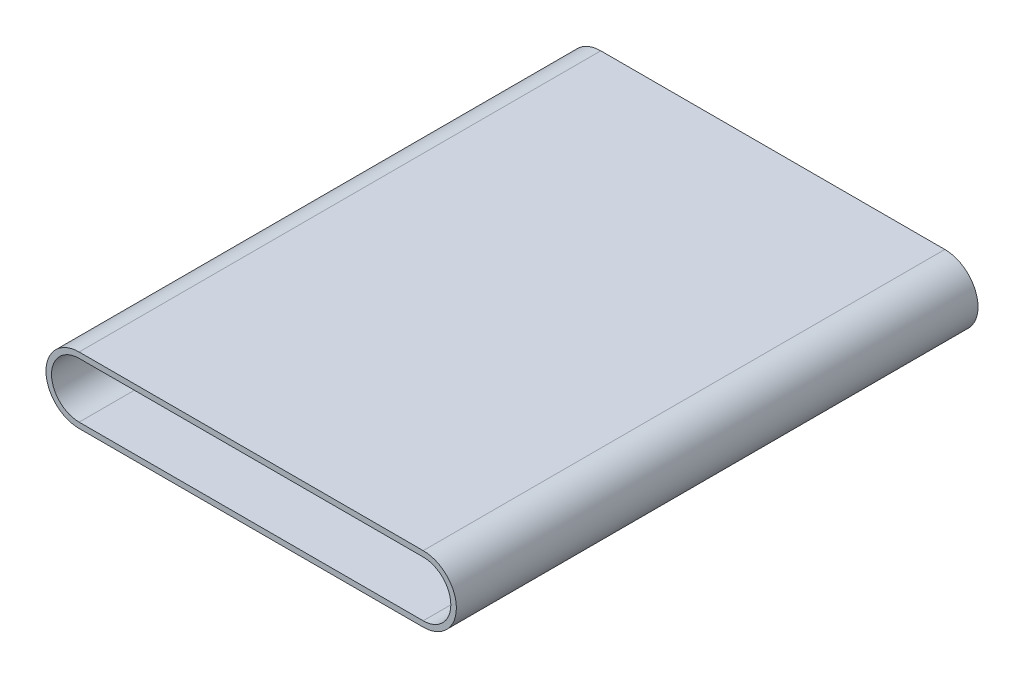
SolidWorks part; units mm, degrees
ref_plane "Front Plane" through (0, 0, 0) normal (0, 0, 1) x (1, 0, 0)
ref_plane "Top Plane" through (0, 0, 0) normal (0, 1, 0) x (1, 0, 0)
ref_plane "Right Plane" through (0, 0, 0) normal (1, 0, 0) x (0, 0, -1)
sketch "Sketch2" plane through (0, 0, 0) normal (0, 0, 1) x (1, 0, 0)
  line L0 (0, 0) -> (1, 0) construction
  line L1 (0, 0) -> (0, 1) construction
  line L2 (0, -24.875) -> (-310, -24.875)
  line L3 (-310, 24.875) -> (0, 24.875)
  arc A0 (0, 24.875) -> (0, -24.875) centre (0, 0) cw
  arc A1 (-310, -24.875) -> (-310, 24.875) centre (-310, 0) cw
sketch "Sketch3" plane through (0, 0, 0) normal (1, 0, 0) x (0, 0, -1)
  line L0 (0, 24.875) -> (0, -24.875) construction
  line L1 (-235, 24.875) -> (235, 24.875)
  line L2 (-235, 24.875) -> (-235, 29.875)
  line L3 (-235, 29.875) -> (235, 29.875)
  line L4 (235, 24.875) -> (235, 29.875)
  dimension "D1" = 235
  dimension "D2" = 235
  dimension "D3" = 5
sweep "Sweep1" add profiles "Sketch3" path "Sketch2"
